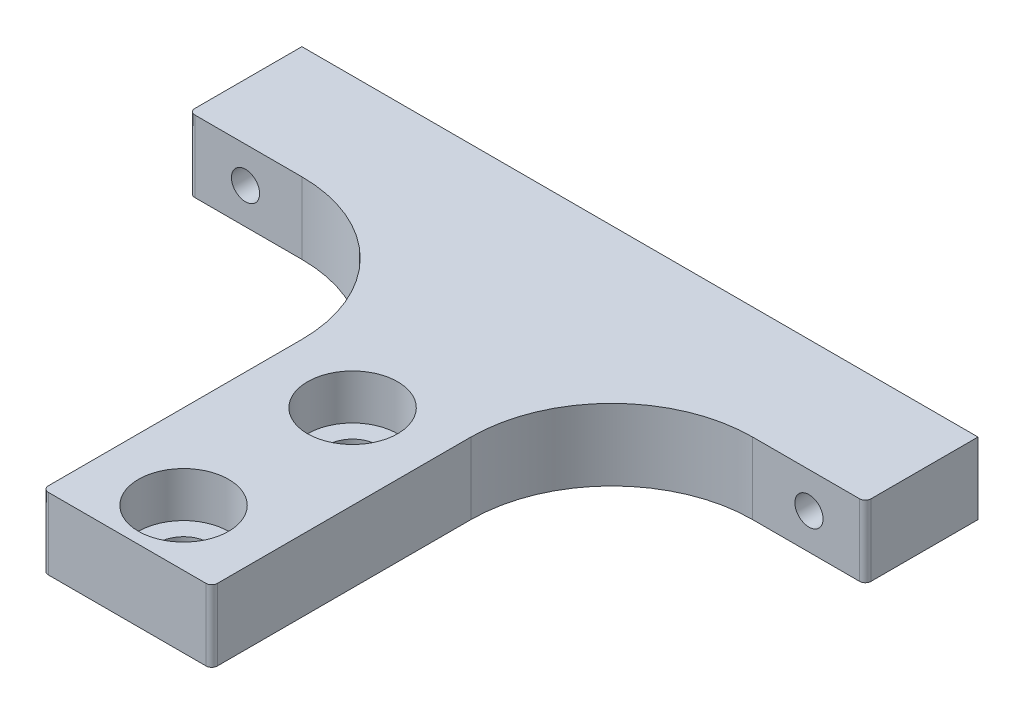
SolidWorks part; units mm, degrees
material "6061-T6 (SS)"
ref_plane "Front Plane" through (0, 0, 0) normal (0, 0, 1) x (1, 0, 0)
ref_plane "Top Plane" through (0, 0, 0) normal (0, 1, 0) x (1, 0, 0)
ref_plane "Right Plane" through (0, 0, 0) normal (1, 0, 0) x (0, 0, -1)
sketch "Sketch2" plane through (0, 0, 0) normal (0, 1, 0) x (1, 0, 0)
  line L0 (-30, 0) -> (30, 0)
  line L1 (-30, 0) -> (-30, -10)
  line L2 (-30, -10) -> (-7.5, -10)
  line L3 (-7.5, -10) -> (-7.5, -45.5)
  line L4 (-7.5, -45.5) -> (7.5, -45.5)
  line L5 (0, 0) -> (0, -45.5) construction
  line L6 (7.5, -10) -> (7.5, -45.5)
  line L7 (30, -10) -> (7.5, -10)
  line L8 (30, 0) -> (30, -10)
  point P4 (0, 0)
  dimension "D1" = 60
  dimension "D2" = 15
  dimension "D3" = 45.5
  dimension "D4" = 10
extrude "Boss-Extrude1" add sketch "Sketch2" along normal blind 6.35
fillet "Fillet1" radius 12.5 2 edges at (7.5, 3.175, 10) (-7.5, 3.175, 10)
sketch "Sketch3" plane through (0, 6.35, 0) normal (0, 1, 0) x (1, 0, 0)
  line L0 (-7.5, -20.5) -> (7.5, -20.5) construction
  line L1 (-7.5, -22.5) -> (-7.5, -45.5) construction
  line L2 (7.5, -45.5) -> (7.5, -22.5) construction
  line L3 (-7.5, -45.5) -> (7.5, -45.5) construction
  line L4 (0, -20.5) -> (0, -45.5) construction
  line L5 (0, -33) -> (10.8574, -33) construction
  point P12 (0, -25.5)
  point P13 (0, -40.5)
  dimension "D1" = 25
  dimension "D2" = 15
hole_wizard "CBORE for M4 SHCS1" positions "Sketch3" profile "Sketch4" counterbore size "M4" standard "ANSI Metric" end condition through all
sketch "Sketch4" plane through (0, 6.35, 40.5) normal (1, 0, 0) x (0, 0, 1)
  line L0 (0, 0) -> (0, 6.35)
  line L1 (0, 6.35) -> (2.25, 6.35)
  line L3 (2.25, 6.35) -> (2.25, 4)
  line L4 (2.25, 4) -> (4, 4)
  line L5 (4, 4) -> (4, 0)
  line L7 (4, 0) -> (0, 0)
  line L11 (0, -6.35) -> (0, 107.95) construction
  dimension "Thru Hole Dia." = 4.5
  dimension "Thru Hole Depth" = 6.35
  dimension "C'Bore Dia." = 8
  dimension "C'Bore Depth" = 4
sketch "Sketch5" plane through (0, 0, 0) normal (0, 0, -1) x (-1, 0, 0)
  line L0 (-30, 3.175) -> (30, 3.175) construction
  line L1 (-30, 6.35) -> (-30, 0) construction
  line L2 (30, 6.35) -> (30, 0) construction
  line L3 (0, 0) -> (0, 6.35) construction
  line L4 (-30, 6.35) -> (30, 6.35) construction
  point P6 (25, 3.175)
  point P12 (-25, 3.175)
  dimension "D1" = 5
hole_wizard "M3x0.5 Tapped Hole1" positions "Sketch5" profile "Sketch6" tap size "M3x0.5" standard "ANSI Metric" end condition up to next
sketch "Sketch6" plane through (25, 3.175, 0) normal (1, 0, 0) x (0, 1, 0)
  line L0 (0, 0) -> (0, 10)
  line L1 (0, 10) -> (1.25, 10)
  line L2 (1.25, 10) -> (1.25, 0)
  line L5 (1.25, 0) -> (0, 0)
  line L11 (0, -6.35) -> (0, 107.95) construction
  dimension "Thru Tap Drill Dia." = 2.5
  dimension "Thru Tap Drill Depth" = 10
fillet "Fillet2" radius 0.5 2 edges at (30, 3.175, 10) (-30, 3.175, 10)
fillet "Fillet3" radius 0.5 2 edges at (7.5, 3.175, 45.5) (-7.5, 3.175, 45.5)
equation "\"D3@Sketch2\"=40.50+5.00"
